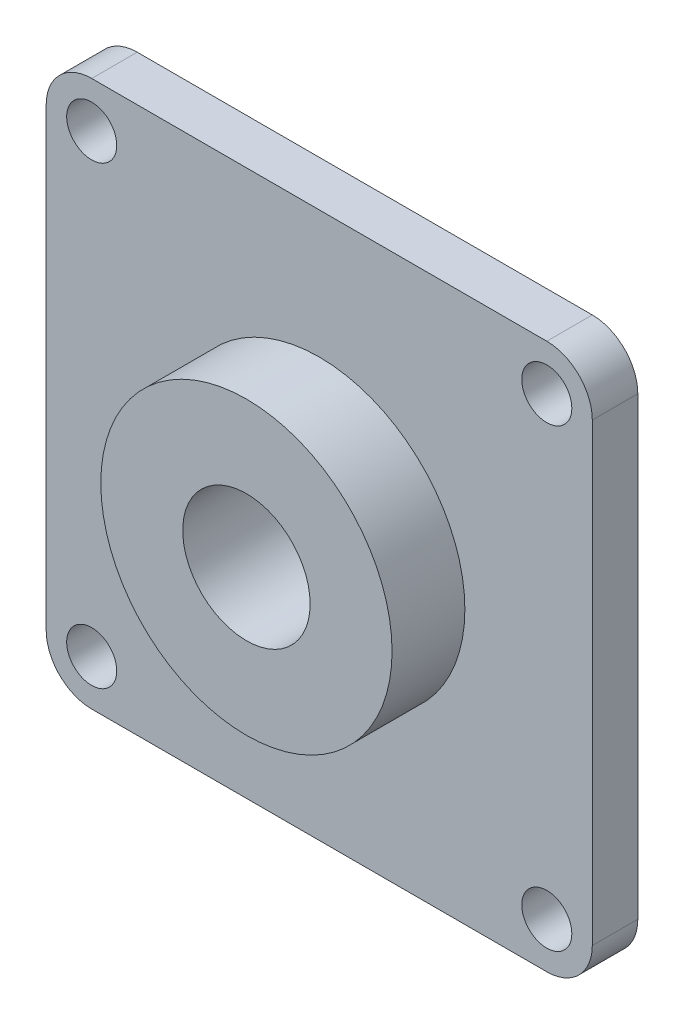
SolidWorks part; units mm, degrees
ref_plane "Front Plane" through (0, 0, 0) normal (0, 0, 1) x (1, 0, 0)
ref_plane "Top Plane" through (0, 0, 0) normal (0, 1, 0) x (1, 0, 0)
ref_plane "Right Plane" through (0, 0, 0) normal (1, 0, 0) x (0, 0, -1)
sketch "Sketch1" plane through (0, 0, 0) normal (0, 0, 1) x (1, 0, 0)
  line L1 (30, 30) -> (-30, 30)
  line L2 (30, 30) -> (30, -30)
  line L3 (30, -30) -> (-30, -30)
  line L4 (-30, 30) -> (-30, -30)
  line L5 (30, 30) -> (-30, -30) construction
  line L6 (30, -30) -> (-30, 30) construction
  point P0 (0, 0)
  dimension "D1" = 60
  dimension "D2" = 60
extrude "Boss-Extrude1" add sketch "Sketch1" along normal blind 5
sketch "Sketch2" plane through (0, 0, 5) normal (0, 0, 1) x (1, 0, 0)
  line L0 (30, 30) -> (-30, 30) construction
  line L13 (-30, 30) -> (-30, -30) construction
  circle A0 centre (-25, 25) radius 2.75
  circle A1 centre (25, 25) radius 2.75
  circle A2 centre (25, -25) radius 2.75
  circle A3 centre (-25, -25) radius 2.75
  dimension "D1" = 5.5
  dimension "D2" = 5
  dimension "D3" = 5
  dimension "D4" = 2
  dimension "D5" = 2
extrude "Cut-Extrude1" cut sketch "Sketch2" against normal blind 5
fillet "Fillet1" radius 5 4 edges at (30, 30, 2.5) (30, -30, 2.5) (-30, -30, 2.5) (-30, 30, 2.5)
sketch "Sketch3" plane through (0, 0, 5) normal (0, 0, 1) x (1, 0, 0)
  circle A0 centre (0, 0) radius 16
  dimension "D1" = 32
extrude "Boss-Extrude2" add sketch "Sketch3" along normal blind 8
sketch "Sketch4" plane through (0, 0, 13) normal (0, 0, 1) x (1, 0, 0)
  circle A0 centre (0, 0) radius 7
  dimension "D1" = 14
extrude "Cut-Extrude2" cut sketch "Sketch4" against normal through all
